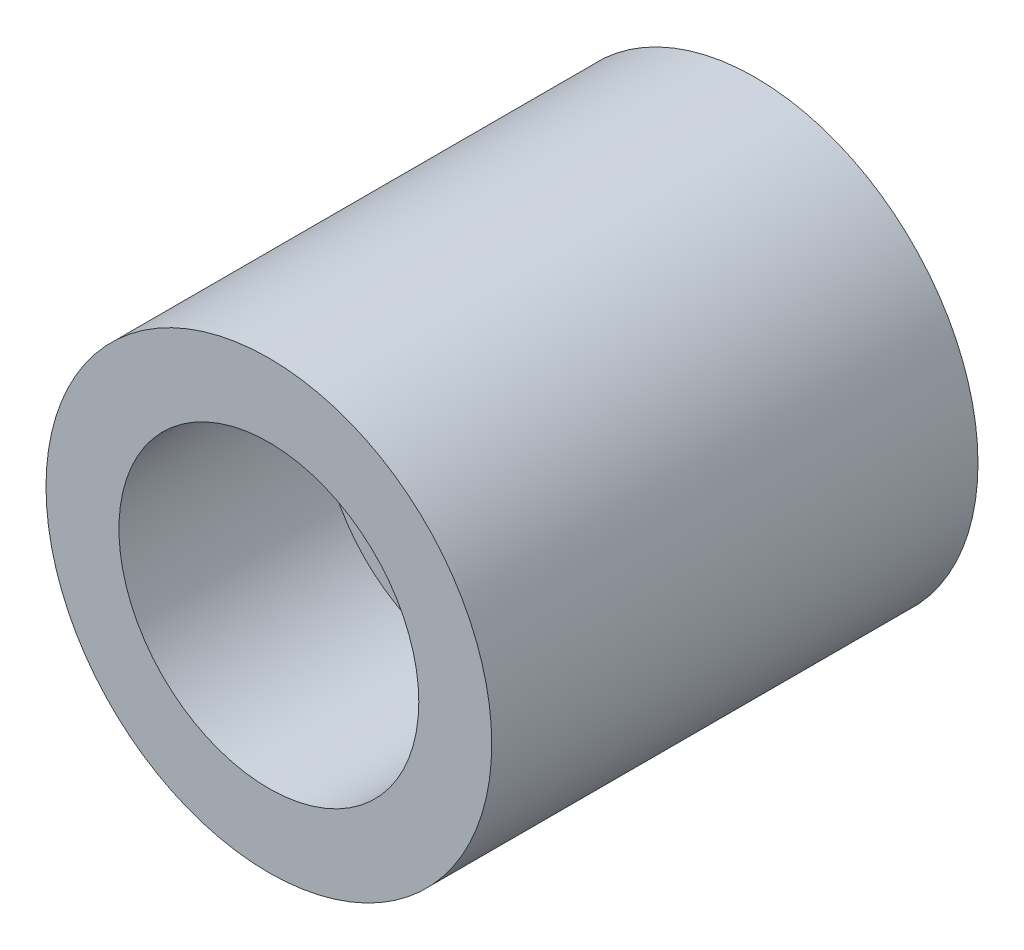
SolidWorks part; units mm, degrees
ref_plane "Přední rovina" through (0, 0, 0) normal (0, 0, 1) x (1, 0, 0)
ref_plane "Horní rovina" through (0, 0, 0) normal (0, 1, 0) x (1, 0, 0)
ref_plane "Pravá rovina" through (0, 0, 0) normal (1, 0, 0) x (0, 0, -1)
sketch "Skica1" plane through (0, 0, 0) normal (0, 0, 1) x (1, 0, 0)
  circle A0 centre (0, 0) radius 2.75
  dimension "D1" = 5.5
extrude "Přidat vysunutím1" add sketch "Skica1" along normal blind 6
sketch "Skica2" plane through (0, 0, 6) normal (0, 0, 1) x (1, 0, 0)
  circle A0 centre (0, 0) radius 1.85
  dimension "D1" = 3.7
extrude "Odebrat vysunutím1" cut sketch "Skica2" against normal blind 2.5
